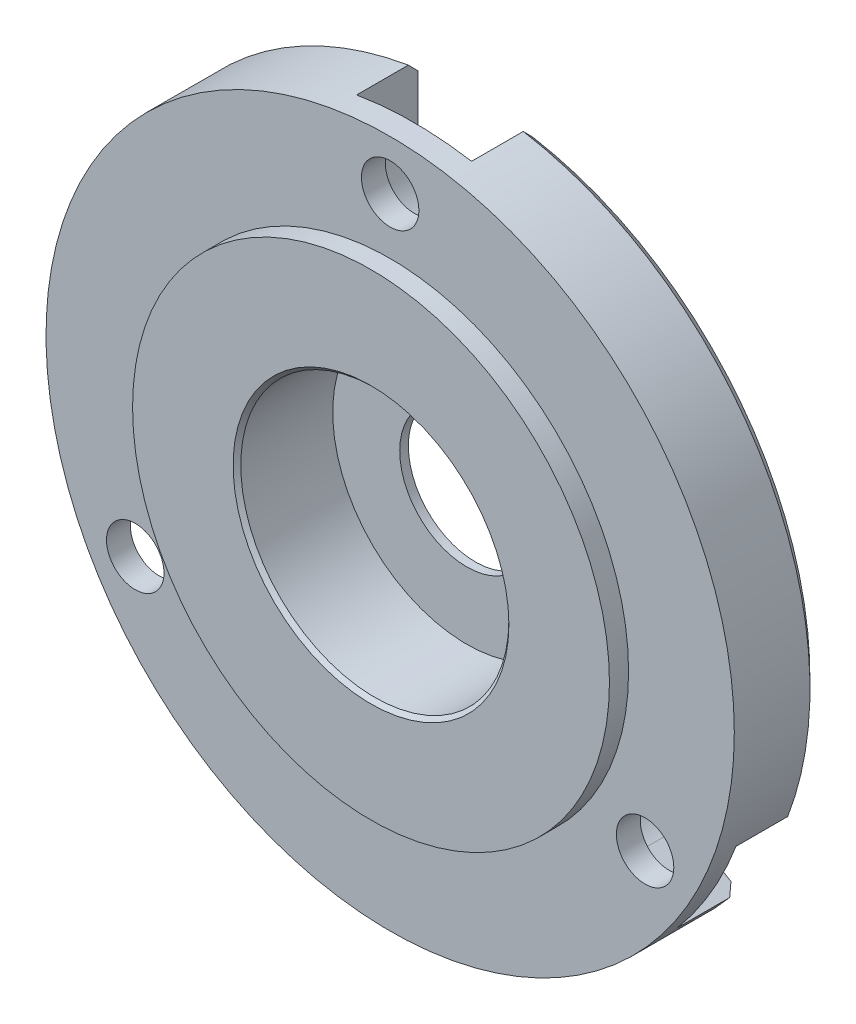
SolidWorks part; units mm, degrees
ref_plane "Plan de face" through (0, 0, 0) normal (0, 0, 1) x (1, 0, 0)
ref_plane "Plan de dessus" through (0, 0, 0) normal (0, 1, 0) x (1, 0, 0)
ref_plane "Plan de droite" through (0, 0, 0) normal (1, 0, 0) x (0, 0, -1)
sketch "Esquisse1" plane through (0, 0, 0) normal (0, 0, 1) x (1, 0, 0)
  circle A0 centre (-74.8422, 51.8721) radius 17.97
extrude "Boss.-Extru.1" add sketch "Esquisse1" along normal blind 4.45
sketch "Esquisse2" plane through (0, 0, 4.45) normal (0, 0, 1) x (1, 0, 0)
  circle A0 centre (-74.8422, 51.8721) radius 12.45
  circle A1 centre (-74.8422, 51.8721) radius 17.97 construction
extrude "Boss.-Extru.2" add sketch "Esquisse2" along normal blind 1
chamfer "Chanfrein1" distance 0.5 angle 45 1 edges at (-56.8722, 51.8721, 0)
sketch "Esquisse5" plane through (0, 0, 0) normal (0, 0, -1) x (-1, 0, 0)
  line L0 (74.8422, 69.8421) -> (74.8422, 32.4297) construction
  line L1 (74.8422, 51.8721) -> (54.6893, 40.2368) construction
  line L2 (56.8722, 51.8721) -> (98.2874, 51.8721) construction
  line L3 (74.8422, 51.8721) -> (95.0822, 40.1865) construction
  circle A0 centre (74.8422, 51.8721) radius 17.97 construction
  circle A1 centre (74.8422, 67.2421) radius 1.5
  circle A2 centre (61.5314, 44.1871) radius 1.5
  circle A3 centre (88.153, 44.1871) radius 1.5
  dimension "D3" = 2.6
  dimension "D4" = 15.37
  dimension "D1" = 30
  dimension "D2" = 30
  dimension "D5" = 15.37
extrude "Enlèv. mat.-Extru.1" cut sketch "Esquisse5" against normal through all
sketch "Esquisse6" plane through (0, 0, 0) normal (0, 0, -1) x (-1, 0, 0)
  circle A0 centre (74.8422, 51.8721) radius 3.5
extrude "Enlèv. mat.-Extru.2" cut sketch "Esquisse6" against normal through all
sketch "Esquisse7" plane through (0, 0, 5.45) normal (0, 0, 1) x (1, 0, 0)
  circle A0 centre (-74.8422, 51.8721) radius 7
extrude "Enlèv. mat.-Extru.3" cut sketch "Esquisse7" against normal blind 5
sketch "Esquisse8" plane through (0, 0, 0) normal (0, 0, -1) x (-1, 0, 0)
  line L0 (71.8422, 70.4119) -> (71.8422, 66.3637)
  line L1 (77.8422, 70.4119) -> (77.8422, 66.3637)
  line L2 (71.8422, 70.4119) -> (77.8422, 70.4119)
  line L3 (60.3796, 39.9252) -> (63.8496, 42.0102)
  line L4 (57.2893, 45.0682) -> (60.7594, 47.1532)
  line L5 (60.3796, 39.9252) -> (57.2893, 45.0682)
  line L6 (92.3713, 45.1334) -> (88.8655, 47.1576)
  line L7 (89.3713, 39.9373) -> (85.8655, 41.9614)
  line L8 (92.3713, 45.1334) -> (89.3713, 39.9373)
  circle A0 centre (74.8422, 67.2421) radius 1.5 construction
  arc A1 (71.8422, 66.3637) -> (77.8422, 66.3637) centre (74.8422, 66.3637) ccw
  arc A2 (63.8496, 42.0102) -> (60.7594, 47.1532) centre (62.3045, 44.5817) ccw
  circle A3 centre (74.8422, 51.8721) radius 17.97 construction
  arc A4 (88.8655, 47.1576) -> (85.8655, 41.9614) centre (87.3655, 44.5595) ccw
  dimension "D1" = 6
  dimension "D2" = 3
  dimension "D3" = 18.55
  dimension "D4" = 18.55
extrude "Enlèv. mat.-Extru.4" cut sketch "Esquisse8" against normal blind 3.2
chamfer "Chanfrein2" distance 0.2 angle 45 1 edges at (-67.8422, 51.8721, 5.45)
